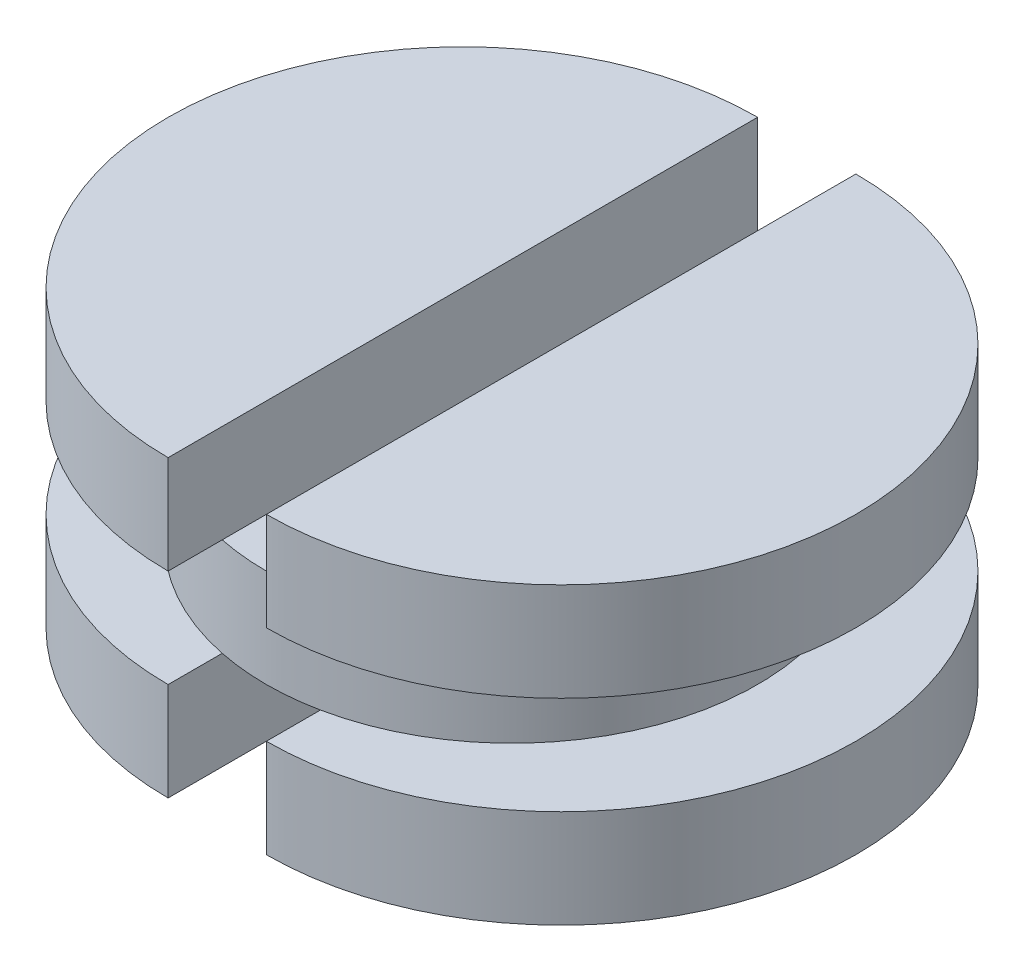
SolidWorks part; units mm, degrees
ref_plane "Front Plane" through (0, 0, 0) normal (0, 0, 1) x (1, 0, 0)
ref_plane "Top Plane" through (0, 0, 0) normal (0, 1, 0) x (1, 0, 0)
ref_plane "Right Plane" through (0, 0, 0) normal (1, 0, 0) x (0, 0, -1)
sketch "Sketch1" plane through (0, 0, 0) normal (0, 1, 0) x (1, 0, 0)
  line L0 (0, -0.6) -> (0, 0.6) construction
  line L1 (4, -0.6) -> (4, 0.6) construction
  line L2 (-4, -0.6) -> (-4, 0.6) construction
  line L3 (0.1, -0.6) -> (0.1, 0.6)
  line L4 (-0.1, -0.6) -> (-0.1, 0.6)
  arc A1 (-0.1, 0.6) -> (-0.1, -0.6) centre (-0.1, 0) ccw
  arc A3 (0.1, -0.6) -> (0.1, 0.6) centre (0.1, 0) ccw
  point P5 (0, 0)
  dimension "D1" = 1.2
  dimension "D2" = 4
  dimension "D3" = 4
  dimension "D4" = 0.1
  dimension "D5" = 0.1
extrude "Boss-Extrude1" add sketch "Sketch1" along normal blind 0.2
sketch "Sketch2" plane through (0, 0.2, 0) normal (0, 1, 0) x (1, 0, 0)
  circle A0 centre (0, 0) radius 0.5
  dimension "D1" = 1
extrude "Boss-Extrude2" add sketch "Sketch2" along normal blind 0.2
sketch "Sketch3" plane through (0, 0.4, 0) normal (0, 1, 0) x (1, 0, 0)
  line L1 (-0.1, -0.6) -> (-0.1, 0.6)
  line L2 (-0.1, -0.6) -> (-0.1, 0.6)
  line L3 (0.1, 0.6) -> (0.1, -0.6)
  line L4 (0.1, 0.6) -> (0.1, -0.6)
  arc A1 (-0.1, 0.6) -> (-0.1, -0.6) centre (-0.1, 0) ccw
  arc A2 (-0.1, 0.6) -> (-0.1, -0.6) centre (-0.1, 0) ccw
  arc A3 (0.1, -0.6) -> (0.1, 0.6) centre (0.1, 0) ccw
  arc A4 (0.1, -0.6) -> (0.1, 0.6) centre (0.1, 0) ccw
  dimension "D1" = 0
  dimension "D2" = 0
extrude "Boss-Extrude3" add sketch "Sketch3" along normal blind 0.2
